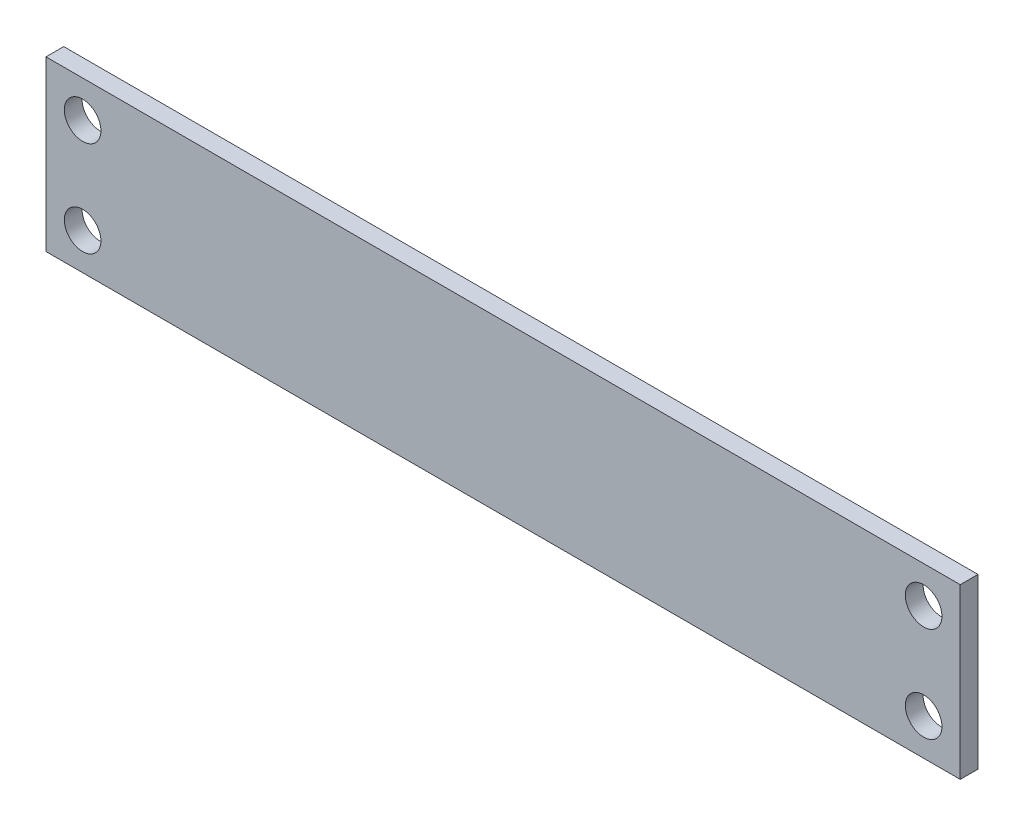
SolidWorks part; units mm, degrees
ref_plane "Спереди" through (0, 0, 0) normal (0, 0, 1) x (1, 0, 0)
ref_plane "Сверху" through (0, 0, 0) normal (0, 1, 0) x (1, 0, 0)
ref_plane "Справа" through (0, 0, 0) normal (1, 0, 0) x (0, 0, -1)
other "Configuration Table"
sketch "Эскиз1" plane through (0, 0, 0) normal (0, 0, 1) x (1, 0, 0)
  line L1 (-41.2, 7.6) -> (41.2, 7.6)
  line L2 (-41.2, 7.6) -> (-41.2, -7.6)
  line L3 (-41.2, -7.6) -> (41.2, -7.6)
  line L4 (41.2, 7.6) -> (41.2, -7.6)
  dimension "D1" = 82.4
  dimension "D2" = 15.2
  dimension "D3" = 41.2
  dimension "D4" = 7.6
extrude "Бобышка-Вытянуть1" add sketch "Эскиз1" along normal blind 1.6
sketch "Эскиз2" plane through (0, 0, 1.6) normal (0, 0, 1) x (1, 0, 0)
  line L0 (41.2, 7.6) -> (-41.2, 7.6) construction
  line L1 (-41.2, 7.6) -> (-41.2, -7.6) construction
  line L2 (-41.2, -7.6) -> (41.2, -7.6) construction
  line L3 (41.2, -7.6) -> (41.2, 7.6) construction
  circle A0 centre (-37.9, 4.3) radius 1.65
  circle A1 centre (-37.9, -4.3) radius 1.65
  circle A2 centre (37.9, 4.3) radius 1.65
  circle A3 centre (37.9, -4.3) radius 1.65
  dimension "D1" = 3.3
  dimension "D2" = 3.3
  dimension "D3" = 3.3
  dimension "D4" = 3.3
  dimension "D5" = 3.3
  dimension "D6" = 3.3
  dimension "D7" = 3.3
  dimension "D8" = 3.3
  dimension "D9" = 3.3
extrude "Вырез-Вытянуть1" cut sketch "Эскиз2" against normal blind 1.6
